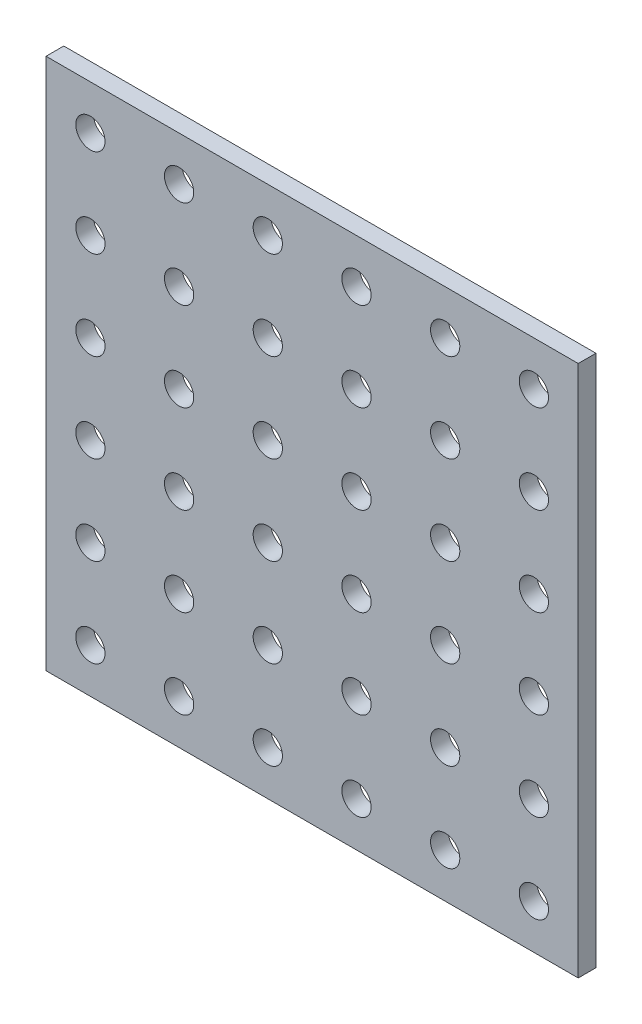
SolidWorks part; units mm, degrees
ref_plane "Front Plane" through (0, 0, 0) normal (0, 0, 1) x (1, 0, 0)
ref_plane "Top Plane" through (0, 0, 0) normal (0, 1, 0) x (1, 0, 0)
ref_plane "Right Plane" through (0, 0, 0) normal (1, 0, 0) x (0, 0, -1)
sketch "Sketch1" plane through (0, 0, 0) normal (0, 0, 1) x (1, 0, 0)
  line L1 (-30, -30) -> (30, -30)
  line L2 (-30, -30) -> (-30, 30)
  line L3 (-30, 30) -> (30, 30)
  line L4 (30, -30) -> (30, 30)
  line L5 (-30, -30) -> (30, 30) construction
  line L6 (-30, 30) -> (30, -30) construction
  point P0 (0, 0)
  dimension "D1" = 60
  dimension "D2" = 60
extrude "Boss-Extrude1" add sketch "Sketch1" along normal blind 2
sketch "Sketch2" plane through (0, 0, 2) normal (0, 0, 1) x (1, 0, 0)
  line L0 (-30, 30) -> (-30, -30) construction
  line L2 (30, 30) -> (-30, 30) construction
  circle A0 centre (-25, 25) radius 1.65
  point P6 (-24.3889, 30)
  dimension "D1" = 3.3
  dimension "D2" = 5
  dimension "D3" = 5
extrude "Cut-Extrude1" cut sketch "Sketch2" against normal through all
pattern_linear "LPattern1" count 6 spacing 10 along (0, -1, 0) count 6 spacing 10 along (1, 0, 0) of "Cut-Extrude1"
